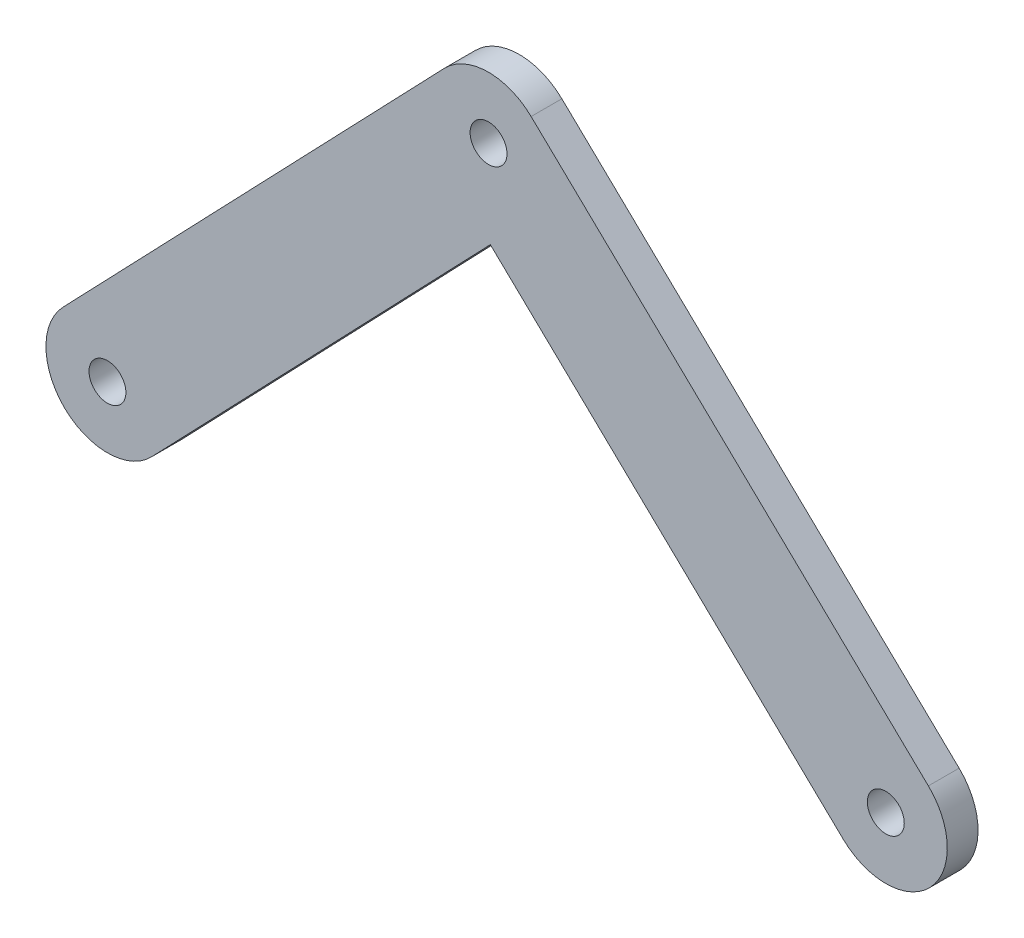
SolidWorks part; units mm, degrees
ref_plane "Front Plane" through (0, 0, 0) normal (0, 0, 1) x (1, 0, 0)
ref_plane "Top Plane" through (0, 0, 0) normal (0, 1, 0) x (1, 0, 0)
ref_plane "Right Plane" through (0, 0, 0) normal (1, 0, 0) x (0, 0, -1)
sketch "Sketch1" plane through (0, 0, 0) normal (0, 0, 1) x (1, 0, 0)
  line L1 (0.2941, -14.1391) -> (-54.7562, -71.5285)
  line L2 (-7.2166, 6.9225) -> (-69.1894, -57.6835)
  line L9 (6.9225, 7.2166) -> (71.5255, -54.7534)
  line L10 (0.2941, -14.1391) -> (57.6805, -69.1866)
  arc A4 (6.9225, 7.2166) -> (-7.2166, 6.9225) centre (0, 0) ccw
  arc A5 (-69.1894, -57.6835) -> (-54.7562, -71.5285) centre (-61.9728, -64.606) ccw
  arc A7 (57.6805, -69.1866) -> (71.5255, -54.7534) centre (64.603, -61.97) ccw
  circle A8 centre (-61.9728, -64.606) radius 3
  circle A9 centre (64.603, -61.97) radius 3
  circle A11 centre (0, 0) radius 3
  point P1 (-30.9864, -32.303)
  point P8 (34.3172, -32.9185)
  dimension "D9" = 6
  dimension "D10" = 6
  dimension "D2" = 6
  dimension "D1" = 90
  dimension "D3" = 10
  dimension "D4" = 10
  dimension "D5" = 89.5241
  dimension "D6" = 89.52
  dimension "D7" = 79.5241
  dimension "D8" = 79.52
extrude "Boss-Extrude2" add sketch "Sketch1" along normal blind 5
